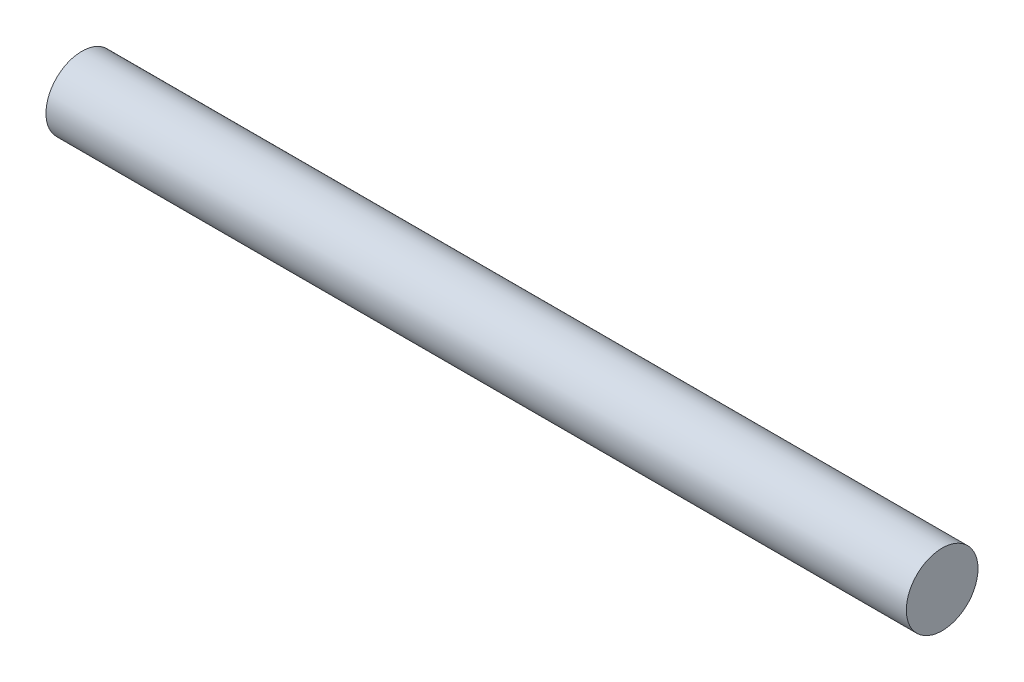
SolidWorks part; units mm, degrees
ref_plane "Front Plane" through (0, 0, 0) normal (0, 0, 1) x (1, 0, 0)
ref_plane "Top Plane" through (0, 0, 0) normal (0, 1, 0) x (1, 0, 0)
ref_plane "Right Plane" through (0, 0, 0) normal (1, 0, 0) x (0, 0, -1)
sketch "Sketch1" plane through (0, 0, 0) normal (1, 0, 0) x (0, 0, -1)
  circle A0 centre (0, 0) radius 2.5
  dimension "D1" = 5
extrude "Boss-Extrude1" add sketch "Sketch1" along normal mid plane 60
